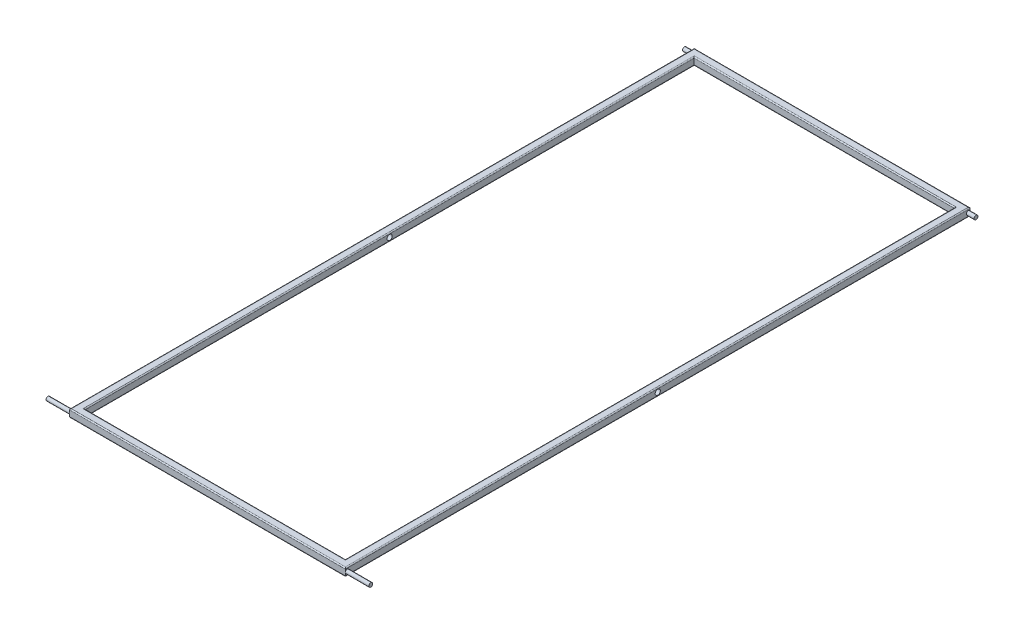
SolidWorks part; units mm, degrees
ref_plane "Alzado" through (0, 0, 0) normal (0, 0, 1) x (1, 0, 0)
ref_plane "Planta" through (0, 0, 0) normal (0, 1, 0) x (1, 0, 0)
ref_plane "Vista lateral" through (0, 0, 0) normal (1, 0, 0) x (0, 0, -1)
sketch "Croquis1" plane through (0, 0, 0) normal (0, 1, 0) x (1, 0, 0)
  line L1 (-265, -600) -> (265, -600)
  line L2 (-265, -600) -> (-265, 600)
  line L3 (-265, 600) -> (265, 600)
  line L4 (265, -600) -> (265, 600)
  line L5 (-265, -600) -> (265, 600) construction
  line L6 (-265, 600) -> (265, -600) construction
  line L7 (-250, -585) -> (250, -585)
  line L8 (-250, -585) -> (-250, 585)
  line L9 (-250, 585) -> (250, 585)
  line L10 (250, -585) -> (250, 585)
  line L11 (-250, -585) -> (250, 585) construction
  line L12 (-250, 585) -> (250, -585) construction
  point P0 (0, 0)
  point P6 (0, 0)
  dimension "D1" = 1200
  dimension "D2" = 530
  dimension "D3" = 500
  dimension "D4" = 1170
extrude "Saliente-Extruir1" add sketch "Croquis1" along normal blind 15
fillet "Redondeo1" radius 2 8 edges at (0, 15, 585) (-250, 15, 0) (0, 15, -585) (250, 15, 0) (265, 15, 0) (0, 15, 600) (-265, 15, 0) (0, 15, -600)
fillet "Redondeo2" radius 2 8 edges at (-250, 0, 0) (0, 0, -585) (250, 0, 0) (0, 0, 585) (0, 0, -600) (-265, 0, 0) (0, 0, 600) (265, 0, 0)
sketch "Croquis2" plane through (-265, 0, 0) normal (-1, 0, 0) x (0, 0, 1)
  line L0 (0, 2) -> (0, 13) construction
  line L1 (-600, 2) -> (600, 2) construction
  line L2 (600, 13) -> (-600, 13) construction
  line L3 (596.25, 2) -> (596.25, 7.5) construction
  line L5 (600, 13) -> (600, 2) construction
  line L6 (596.25, 7.5) -> (600, 7.5) construction
  circle A0 centre (596.25, 7.5) radius 3.75
  circle A1 centre (-596.25, 7.5) radius 3.75
  dimension "D2" = 7.5
  dimension "D1" = 3.75
extrude "Saliente-Extruir2" add sketch "Croquis2" along normal blind 15
mirror "Simetría1" about plane through (0, 0, 0) normal (1, 0, 0) of "Saliente-Extruir2"
sketch "Croquis3" plane through (-265, 0, 0) normal (-1, 0, 0) x (0, 0, 1)
  line L0 (0, 2) -> (0, 13) construction
  line L1 (-600, 2) -> (600, 2) construction
  line L2 (600, 13) -> (-600, 13) construction
  circle A0 centre (0, 7.5) radius 5
  dimension "D1" = 10
extrude "Cortar-Extruir1" cut sketch "Croquis3" against normal through all
sketch "Croquis4" plane through (280, 0, 0) normal (1, 0, 0) x (0, 0, -1)
  circle A0 centre (-596.25, 7.5) radius 3.75
extrude "Saliente-Extruir3" add sketch "Croquis4" along normal blind 30
sketch "Croquis5" plane through (-280, 0, 0) normal (-1, 0, 0) x (0, 0, 1)
  circle A0 centre (596.25, 7.5) radius 3.75
extrude "Saliente-Extruir4" add sketch "Croquis5" along normal blind 30
scale "Escala1" scale about origin uniform scaling yes scale factor 1.3
